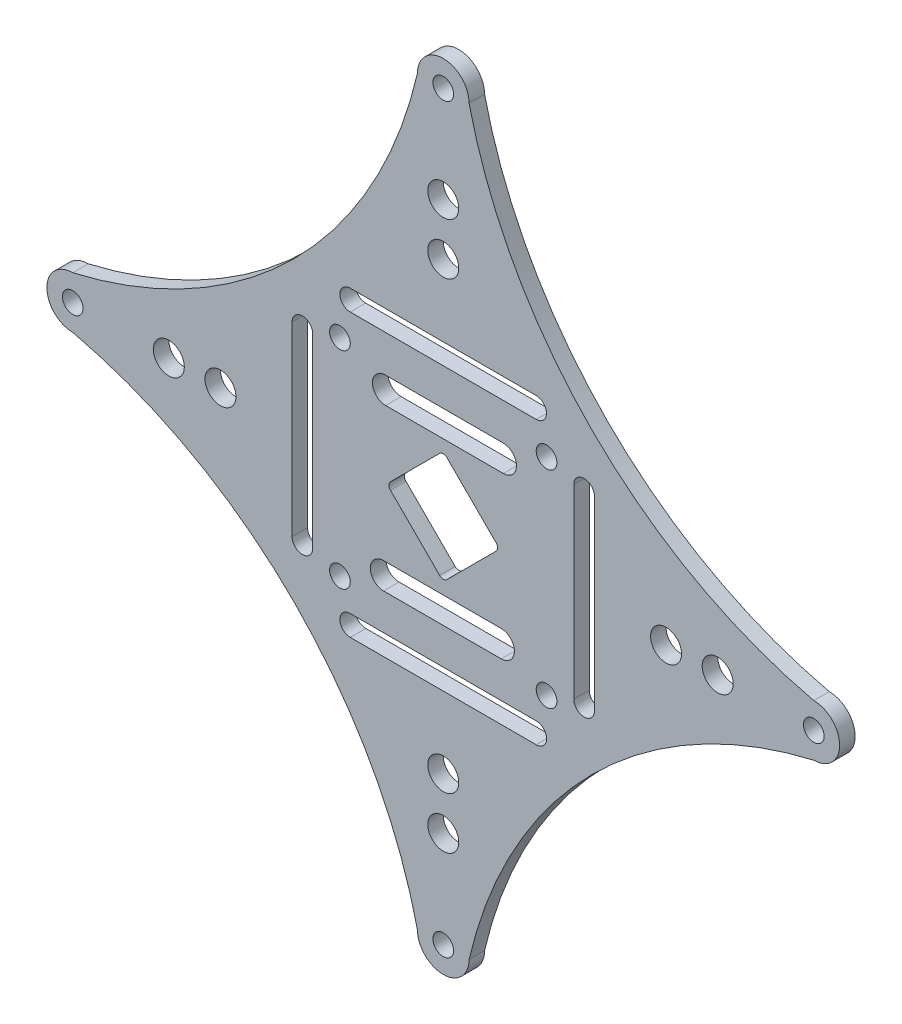
SolidWorks part; units mm, degrees
material "Hexcel AS4C (3000 丝)"
ref_plane "前视基准面" through (0, 0, 0) normal (0, 0, 1) x (1, 0, 0)
ref_plane "上视基准面" through (0, 0, 0) normal (0, 1, 0) x (1, 0, 0)
ref_plane "右视基准面" through (0, 0, 0) normal (1, 0, 0) x (0, 0, -1)
sketch "Model" plane through (0, 0, 0) normal (0, 0, 1) x (1, 0, 0)
  line L0 (40.8955, 64.1152) -> (58.8955, 64.1152)
  line L1 (58.8955, 66.1152) -> (40.8955, 66.1152)
  line L2 (37.2665, 42.4715) -> (37.2665, 60.4715)
  line L3 (35.2665, 60.4715) -> (35.2665, 42.4715)
  line L4 (58.9101, 38.8425) -> (40.9101, 38.8425)
  line L5 (40.9101, 36.8425) -> (58.9101, 36.8425)
  line L6 (62.5392, 60.4862) -> (62.5392, 42.4862)
  line L7 (64.5392, 42.4862) -> (64.5392, 60.4862)
  line L8 (55.5141, 42.346) -> (44.1203, 42.346)
  line L9 (44.1203, 44.893) -> (55.5141, 44.893)
  line L10 (55.7153, 60.5383) -> (44.3215, 60.5383)
  line L11 (44.3215, 57.9913) -> (55.7153, 57.9913)
  line L12 (55.0142, 51.8324) -> (50.2564, 56.5902)
  line L13 (49.5493, 56.5902) -> (44.7915, 51.8324)
  line L14 (44.7915, 51.1253) -> (49.5493, 46.3675)
  line L15 (50.2564, 46.3675) -> (55.0142, 51.1253)
  line L16 (40.8955, 38.8425) -> (58.8955, 38.8425)
  line L17 (58.8955, 36.8425) -> (40.8955, 36.8425)
  circle A0 centre (85.7715, 51.4789) radius 1
  arc A1 (85.7715, 48.9789) -> (85.7715, 53.9789) centre (85.7715, 51.4789) ccw
  circle A2 centre (14.0341, 51.4789) radius 1
  arc A3 (14.0341, 53.9789) -> (14.0341, 48.9789) centre (14.0341, 51.4789) ccw
  circle A4 centre (49.9028, 87.3759) radius 1
  arc A5 (52.4028, 87.3759) -> (47.4028, 87.3759) centre (49.9028, 87.3759) ccw
  circle A6 centre (49.9028, 15.5818) radius 1
  arc A7 (47.4028, 15.5818) -> (52.4028, 15.5818) centre (49.9028, 15.5818) ccw
  arc A8 (14.0341, 53.9789) -> (47.4028, 87.3759) centre (3.921, 97.4521) ccw
  arc A9 (52.4028, 87.3759) -> (85.7715, 53.9789) centre (95.8846, 97.4521) ccw
  arc A10 (47.4028, 15.5818) -> (14.0341, 48.9789) centre (3.921, 5.5057) ccw
  arc A11 (85.7715, 48.9789) -> (52.4028, 15.5818) centre (95.8846, 5.5057) ccw
  circle A12 centre (59.9028, 61.4789) radius 1
  circle A13 centre (39.9028, 61.4789) radius 1
  circle A14 centre (39.9028, 41.4789) radius 1
  circle A15 centre (59.9028, 41.4789) radius 1
  circle A16 centre (71.4696, 51.4789) radius 1.5
  circle A17 centre (49.9028, 73.0456) radius 1.5
  circle A18 centre (28.3361, 51.4789) radius 1.5
  circle A19 centre (49.9028, 29.9121) radius 1.5
  circle A20 centre (49.9028, 78.0456) radius 1.5
  circle A21 centre (23.3361, 51.4789) radius 1.5
  circle A22 centre (49.9028, 24.9121) radius 1.5
  circle A23 centre (76.4696, 51.4789) radius 1.5
  arc A24 (39.8955, 65.1152) -> (40.8955, 64.1152) centre (40.8955, 65.1152) ccw
  arc A25 (58.8955, 64.1152) -> (58.8955, 66.1152) centre (58.8955, 65.1152) ccw
  arc A26 (40.8955, 66.1152) -> (39.8955, 65.1152) centre (40.8955, 65.1152) ccw
  arc A27 (36.2665, 41.4715) -> (37.2665, 42.4715) centre (36.2665, 42.4715) ccw
  arc A28 (37.2665, 60.4715) -> (35.2665, 60.4715) centre (36.2665, 60.4715) ccw
  arc A29 (35.2665, 42.4715) -> (36.2665, 41.4715) centre (36.2665, 42.4715) ccw
  arc A30 (59.9101, 37.8425) -> (58.9101, 38.8425) centre (58.9101, 37.8425) ccw
  arc A31 (40.9101, 38.8425) -> (40.9101, 36.8425) centre (40.9101, 37.8425) ccw
  arc A32 (58.9101, 36.8425) -> (59.9101, 37.8425) centre (58.9101, 37.8425) ccw
  arc A33 (63.5392, 61.4862) -> (62.5392, 60.4862) centre (63.5392, 60.4862) ccw
  arc A34 (62.5392, 42.4862) -> (64.5392, 42.4862) centre (63.5392, 42.4862) ccw
  arc A35 (64.5392, 60.4862) -> (63.5392, 61.4862) centre (63.5392, 60.4862) ccw
  arc A36 (42.8468, 43.6195) -> (44.1203, 42.346) centre (44.1203, 43.6195) ccw
  arc A37 (55.5141, 42.346) -> (55.5141, 44.893) centre (55.5141, 43.6195) ccw
  arc A38 (44.1203, 44.893) -> (42.8468, 43.6195) centre (44.1203, 43.6195) ccw
  arc A39 (44.3215, 60.5383) -> (43.048, 59.2648) centre (44.3215, 59.2648) ccw
  arc A40 (55.7153, 57.9913) -> (55.7153, 60.5383) centre (55.7153, 59.2648) ccw
  arc A41 (43.048, 59.2648) -> (44.3215, 57.9913) centre (44.3215, 59.2648) ccw
  arc A42 (55.0142, 51.1253) -> (55.0142, 51.8324) centre (54.6606, 51.4789) ccw
  arc A43 (50.2564, 56.5902) -> (49.5493, 56.5902) centre (49.9028, 56.2367) ccw
  arc A44 (44.7915, 51.8324) -> (44.7915, 51.1253) centre (45.145, 51.4789) ccw
  arc A45 (49.5493, 46.3675) -> (50.2564, 46.3675) centre (49.9028, 46.7211) ccw
  arc A46 (40.8955, 38.8425) -> (39.8955, 37.8425) centre (40.8955, 37.8425) ccw
  arc A47 (58.8955, 36.8425) -> (58.8955, 38.8425) centre (58.8955, 37.8425) ccw
  arc A48 (39.8955, 37.8425) -> (40.8955, 36.8425) centre (40.8955, 37.8425) ccw
  spline S0 degree 3 poles (0, 0) (0.3333, 0) (0.6667, 0) (1, 0) knots 0 0 0 0 1 1 1 1
  spline S1 degree 3 poles (0, 0) (0.3333, 0) (0.6667, 0) (1, 0) knots 0 0 0 0 1 1 1 1
extrude "凸台-拉伸1" add sketch "Model" along normal blind 1.5 contours S0 S1 | A6 | A4 | A2 | A1 A9 A5 A8 A3 A10 A7 A11 | A0 | A16 | A15 | A14 | A13 | A12 | A23 | A22 | A21 | A20 | A19 | A18 | A17 | L4 A31 L5 A32 A30 | L2 A28 L3 A29 A27 | L0 A25 L1 A26 A24 | L8 A36 A38 L9 A37 | L6 A34 L7 A35 A33 | L12 A43 L13 A44 L14 A45 L15 A42 | L10 A39 A41 L11 A40 | L16 A47 L17 A48 A46
